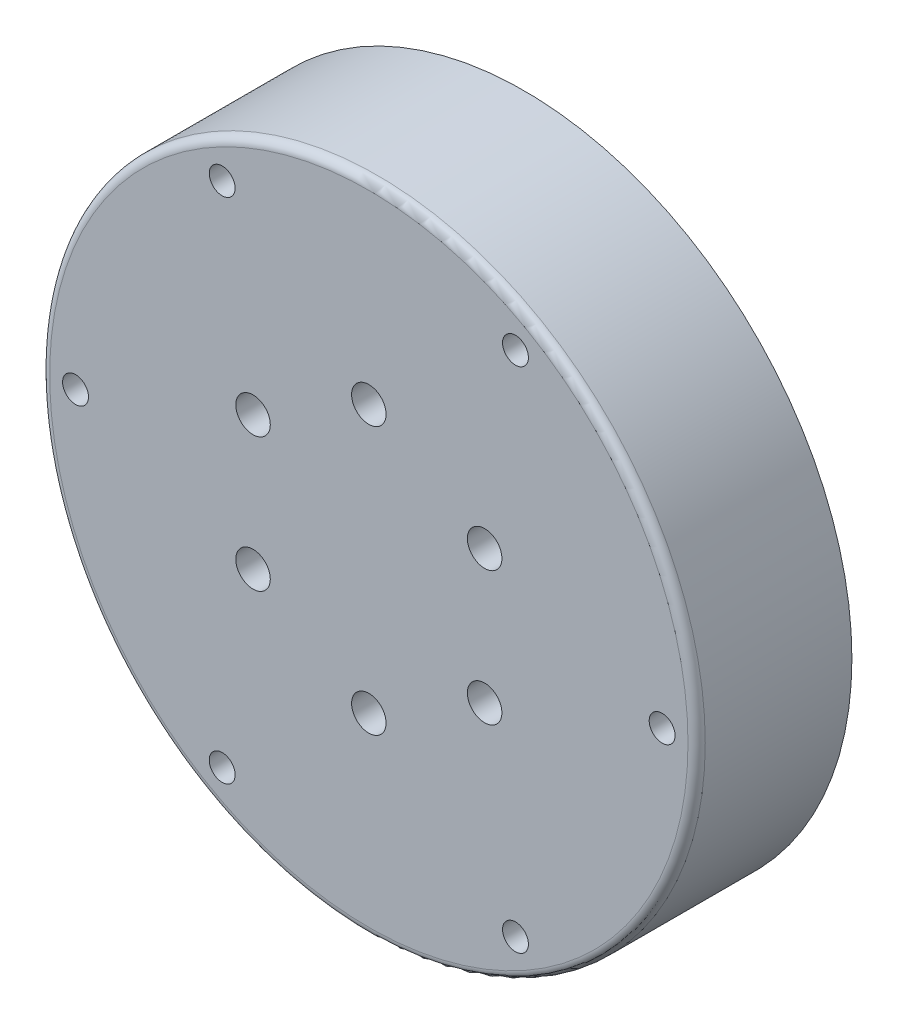
SolidWorks part; units mm, degrees
material "ABS"
ref_plane "Спереди" through (0, 0, 0) normal (0, 0, 1) x (1, 0, 0)
ref_plane "Сверху" through (0, 0, 0) normal (0, 1, 0) x (1, 0, 0)
ref_plane "Справа" through (0, 0, 0) normal (1, 0, 0) x (0, 0, -1)
other "Configuration Table"
sketch "Эскиз1" plane through (0, 0, 0) normal (0, 0, 1) x (1, 0, 0)
  circle A0 centre (0, 0) radius 38
  dimension "D1" = 76
extrude "Бобышка-Вытянуть1" add sketch "Эскиз1" along normal blind 18
sketch "Эскиз2" plane through (0, 0, 18) normal (0, 0, 1) x (1, 0, 0)
  line L0 (0, 0) -> (-34, 0) construction
  line L1 (0, 0) -> (-17, 29.4449) construction
  circle A0 centre (0, 0) radius 34 construction
  circle A1 centre (-34, 0) radius 1.5
  circle A2 centre (0, 0) radius 34 construction
  circle A3 centre (-17, 29.4449) radius 1.5
  circle A4 centre (0, 0) radius 34 construction
  circle A5 centre (17, 29.4449) radius 1.5
  circle A6 centre (0, 0) radius 34 construction
  circle A7 centre (34, 0) radius 1.5
  circle A8 centre (0, 0) radius 34 construction
  circle A9 centre (17, -29.4449) radius 1.5
  circle A10 centre (0, 0) radius 34 construction
  circle A11 centre (-17, -29.4449) radius 1.5
  dimension "D1" = 68
  dimension "D2" = 3
  dimension "D4" = 60
  dimension "D3" = 6
extrude "Вырез-Вытянуть1" cut sketch "Эскиз2" against normal up to next contours A7 | A5 | A3 | A1 | A11 | A9
sketch "Эскиз3" plane through (0, 0, 0) normal (0, 0, -1) x (-1, 0, 0)
  line L0 (-13.0767, -27) -> (13.0767, -27)
  arc A0 (13.0767, -27) -> (-13.0767, -27) centre (0, 0) ccw
  dimension "D1" = 60
  dimension "D2" = 27
extrude "Вырез-Вытянуть2" cut sketch "Эскиз3" against normal blind 12.5
fillet "Скругление1" radius 1 1 edges at (38, 0, 18)
ref_plane "Плоскость1" through (0, -27, 0) normal (0, 1, 0) x (1, 0, 0)
sketch "Эскиз6" plane through (0, -27, 0) normal (0, 1, 0) x (1, 0, 0)
  line L0 (38, 0) -> (-38, 0) construction
  line L1 (-10, -8.5) -> (10, -8.5)
  line L2 (-10, -8.5) -> (-10, -12.5)
  line L3 (-10, -12.5) -> (10, -12.5)
  line L4 (10, -8.5) -> (10, -12.5)
  line L5 (-10, -8.5) -> (10, -12.5) construction
  line L6 (-10, -12.5) -> (10, -8.5) construction
  line L7 (0, 24) -> (0, -24) construction
  point P0 (0, -10.5)
  point P11 (0, 0)
  dimension "D1" = 4
  dimension "D2" = 20
  dimension "D3" = 8.5
  dimension "D4" = 10
extrude "Вырез-Вытянуть7" cut sketch "Эскиз6" against normal up to next
sketch "Эскиз7" plane through (0, 0, 18) normal (0, 0, 1) x (1, 0, 0)
  line L0 (0, 0) -> (0, 15.5) construction
  circle A1 centre (0, 0) radius 15.5 construction
  circle A2 centre (0, 15.5) radius 2
  circle A4 centre (13.4234, 7.75) radius 2
  circle A6 centre (13.4234, -7.75) radius 2
  circle A8 centre (0, -15.5) radius 2
  circle A10 centre (-13.4234, -7.75) radius 2
  circle A12 centre (-13.4234, 7.75) radius 2
  circle A13 centre (0, 0) radius 15.5 [skipped]
  circle A14 centre (0, 0) radius 15.5 [skipped]
  circle A15 centre (0, 0) radius 15.5 [skipped]
  circle A16 centre (0, 0) radius 15.5 [skipped]
  circle A17 centre (0, 0) radius 15.5 [skipped]
  point P4 (0, 0)
  dimension "D3" = 6
  dimension "D1" = 31
  dimension "D2" = 4
extrude "Вырез-Вытянуть8" cut sketch "Эскиз7" against normal up to next
